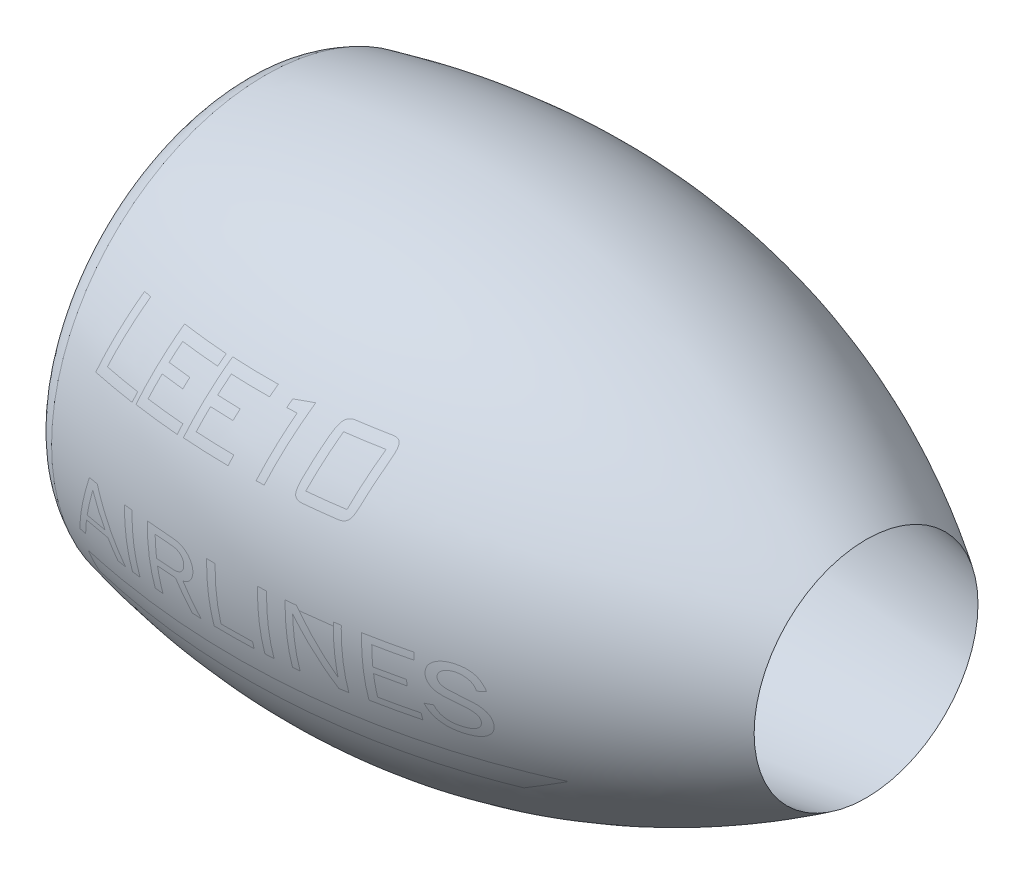
SolidWorks part; units mm, degrees
ref_plane "Front Plane" through (0, 0, 0) normal (0, 0, 1) x (1, 0, 0)
ref_plane "Top Plane" through (0, 0, 0) normal (0, 1, 0) x (1, 0, 0)
ref_plane "Right Plane" through (0, 0, 0) normal (1, 0, 0) x (0, 0, -1)
sketch "Sketch1" plane through (0, 0, 0) normal (0, 0, 1) x (1, 0, 0)
  line L0 (0, 0) -> (580, 0) construction
  line L1 (0, 0) -> (0, 447.1127) construction
  line L2 (0, 180) -> (25, 180)
  line L3 (25, 180) -> (35.2784, 190)
  line L4 (35.2784, 190) -> (86.9735, 190)
  line L5 (580, 108) -> (86.9735, 190)
  spline S0 degree 2 poles (0, 205.8469) (312.95, 281.233) (580, 108) knots 0 0 0 1 1 1
  spline S1 degree 2 poles (0, 205.8469) (-35.1751, 189.0954) (0, 180) knots 0 0 0 1 1 1
  point P8 (0, 278.8534)
  point P13 (-25.4399, 207.2926)
  point P14 (0, 221.7493)
  point P15 (322.2444, 215.2438)
  point P16 (0, 0)
  point P17 (0, 0)
  point P18 (-18.2115, 197.8957)
  point P19 (0, 205.8469)
  point P20 (-12.4288, 190)
  point P21 (35.2784, 190)
  point P22 (-17.4777, 190)
  point P23 (86.9735, 190)
  dimension "D1" = 108
  dimension "D2" = 580
  dimension "D3" = 180
  dimension "D4" = 190
  dimension "D5" = 25
revolve "Revolve1" add sketch "Sketch1" angle 360 about L0
ref_plane "Plane1" through (0, 0, 250) normal (0, 0, 1) x (1, 0, 0)
sketch "Sketch2" plane through (0, 0, 250) normal (0, 0, 1) x (1, 0, 0)
  line L0 (24.8004, 76.1245) -> (469.1817, 80.7615) construction
  line L1 (24.8004, -59.122) -> (469.1817, -53.7122) construction
  line L2 (449.8608, -80.7615) -> (410.4461, -103.9466)
  line L3 (24.8004, -103.9466) -> (410.4461, -103.9466)
  line L4 (24.8004, -103.9466) -> (24.8004, -80.7615)
  line L5 (24.8004, -80.7615) -> (449.8608, -80.7615)
  text T0 "LEE10 " font "BankGothic Lt BT" height 60
  text T1 "AIRLINES" font "Franklin Gothic Book" height 60
split line "Split Line2"
